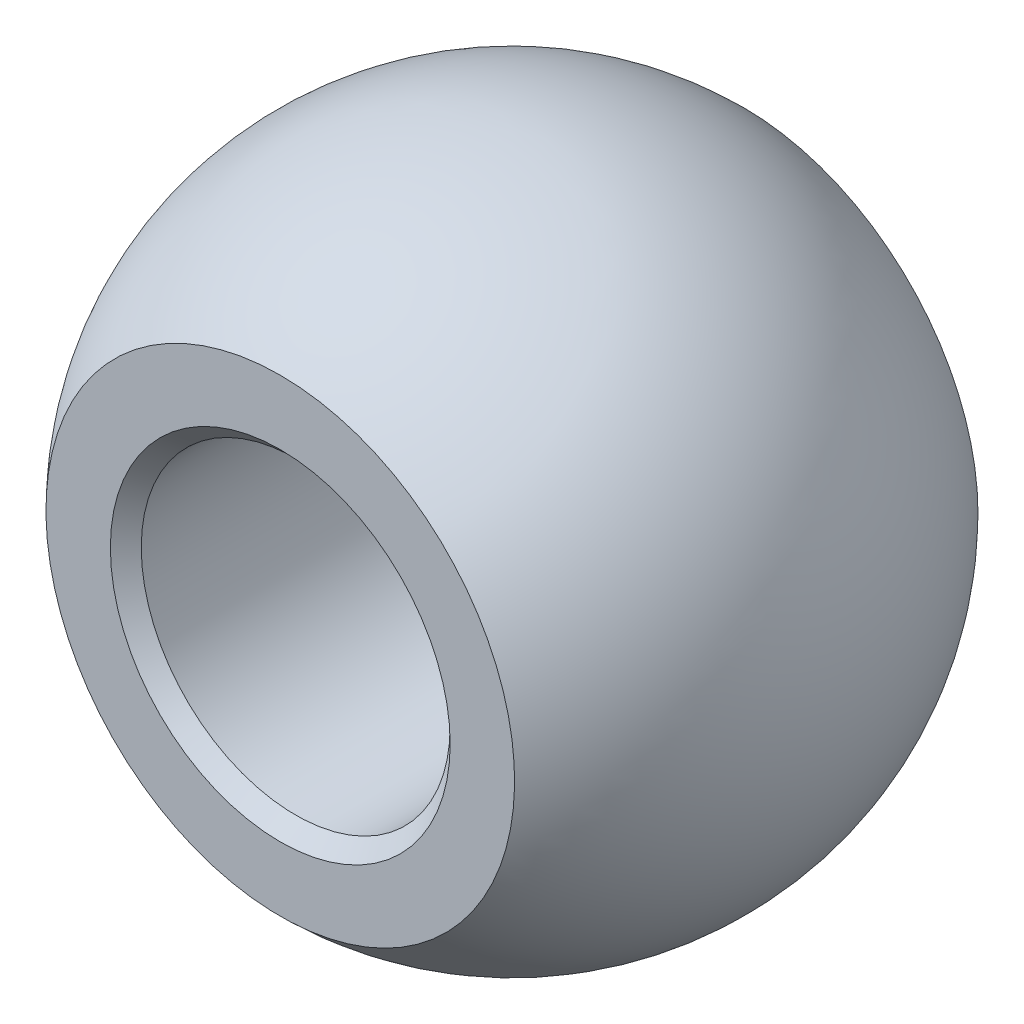
SolidWorks part; units mm, degrees
ref_plane "Спереди" through (0, 0, 0) normal (0, 0, 1) x (1, 0, 0)
ref_plane "Сверху" through (0, 0, 0) normal (0, 1, 0) x (1, 0, 0)
ref_plane "Справа" through (0, 0, 0) normal (1, 0, 0) x (0, 0, -1)
sketch "Эскиз1" plane through (0, 0, 0) normal (0, 0, 1) x (1, 0, 0)
  line L0 (0, 6.4) -> (0, 3)
  line L1 (0, -3) -> (0, -6.4)
  line L2 (0, 3) -> (0, -3)
  arc A0 (0, 6.4) -> (0, -6.4) centre (0, 0) ccw
  dimension "D1" = 12.8
revolve "Повернуть1" add sketch "Эскиз1" angle 360 about L0
sketch "Эскиз2" plane through (0, 0, 0) normal (1, 0, 0) x (0, 0, -1)
  line L1 (4.5, 7.9083) -> (10.1653, 7.9083)
  line L2 (4.5, 7.9083) -> (4.5, -7.9492)
  line L3 (4.5, -7.9492) -> (10.1653, -7.9492)
  line L4 (10.1653, 7.9083) -> (10.1653, -7.9492)
  line L5 (-4.5, 8.4504) -> (-10.328, 8.4504)
  line L6 (-4.5, 8.4504) -> (-4.5, -8.654)
  line L7 (-4.5, -8.654) -> (-10.328, -8.654)
  line L8 (-10.328, 8.4504) -> (-10.328, -8.654)
  circle A0 centre (0, 0) radius 6.4 construction
  dimension "D1" = 4.5
  dimension "D2" = 9
extrude "Вырез-Вытянуть1" cut sketch "Эскиз2" against normal through all and the other way through all
sketch "Эскиз3" plane through (0, 0, 4.5) normal (0, 0, 1) x (1, 0, 0)
  circle A0 centre (0, 0) radius 3
extrude "Вырез-Вытянуть2" cut sketch "Эскиз3" against normal through all
chamfer "Фаска1" distance 0.3 angle 45 2 edges at (3, 0, 4.5) (3, 0, -4.5)
